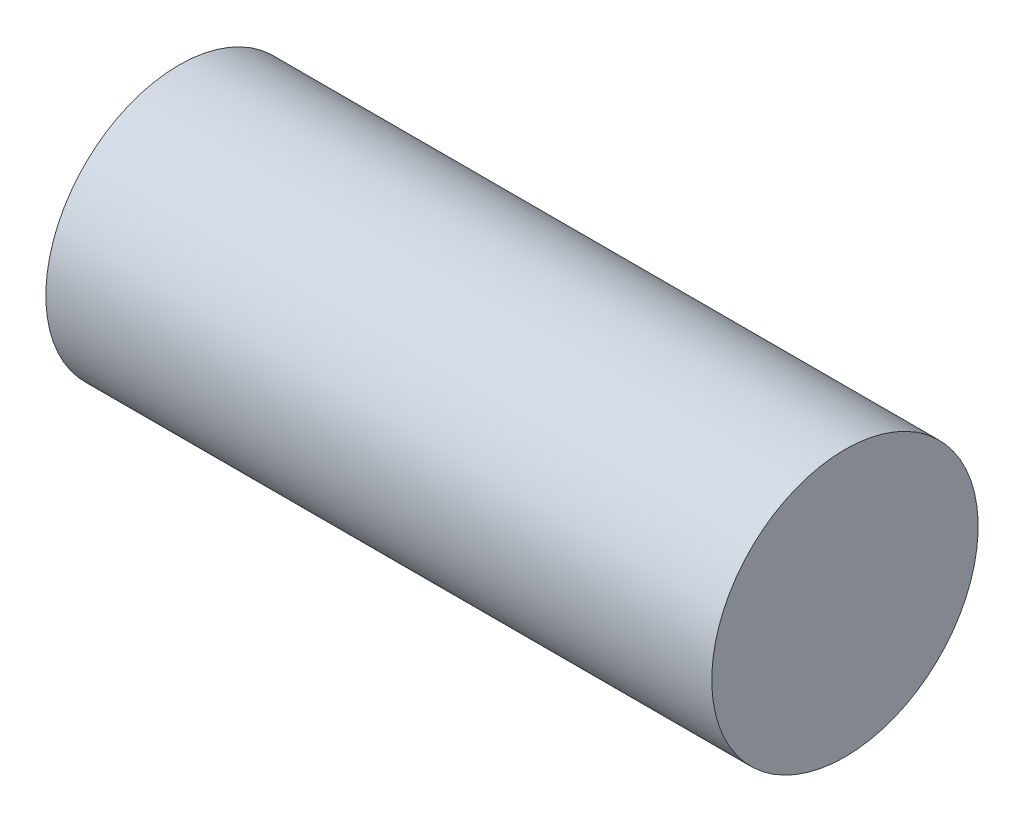
SolidWorks part; units mm, degrees
ref_plane "Front Plane" through (0, 0, 0) normal (0, 0, 1) x (1, 0, 0)
ref_plane "Top Plane" through (0, 0, 0) normal (0, 1, 0) x (1, 0, 0)
ref_plane "Right Plane" through (0, 0, 0) normal (1, 0, 0) x (0, 0, -1)
sketch "Sketch2" plane through (0, 0, 0) normal (0, 0, 1) x (1, 0, 0)
  line L0 (5, 0) -> (5, 150)
  line L1 (-5, 0) -> (-5, 150)
  line L2 (-75, -5) -> (75, -5)
  arc A0 (-5, 0) -> (5, 0) centre (0, 0) ccw
  point P9 (0, -5)
sweep "Sweep1" add path "Sketch2" circular profile diameter 60 parameters "D3"=60
